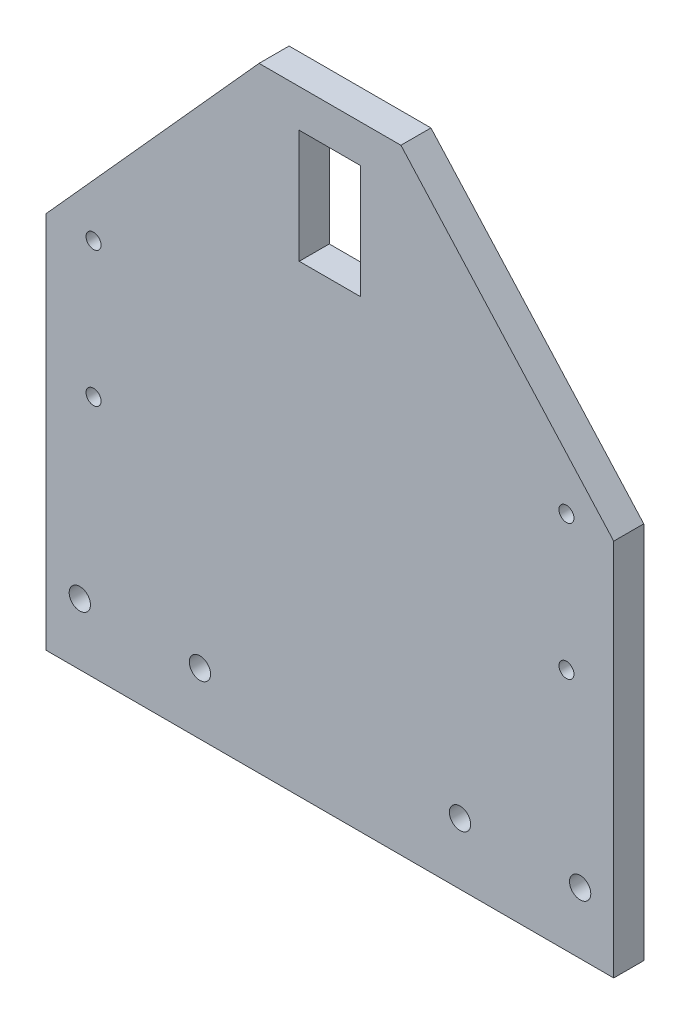
SolidWorks part; units mm, degrees
material "Cast Alloy Steel"
ref_plane "Front Plane" through (0, 0, 0) normal (0, 0, 1) x (1, 0, 0)
ref_plane "Top Plane" through (0, 0, 0) normal (0, 1, 0) x (1, 0, 0)
ref_plane "Right Plane" through (0, 0, 0) normal (1, 0, 0) x (0, 0, -1)
sketch "Sketch1" plane through (0, 0, 0) normal (0, 0, 1) x (1, 0, 0)
  line L0 (60, 0) -> (-60, 0)
  line L1 (0, 80) -> (0, 0) construction
  line L2 (-60, 0) -> (-60, 80)
  line L3 (60, 0) -> (60, 80)
  line L4 (60, 80) -> (15, 130)
  line L5 (15, 130) -> (-15, 130)
  line L6 (-15, 130) -> (-60, 80)
  point P3 (0, 130)
  dimension "D2" = 50
  dimension "D3" = 80
  dimension "D1" = 60
  dimension "D4" = 45
extrude "Boss-Extrude1" add sketch "Sketch1" along normal mid plane 6.35
sketch "Sketch3" plane through (0, 0, 3.175) normal (0, 0, 1) x (1, 0, 0)
  line L0 (15, 130) -> (-15, 130) construction
  line L1 (-60, 0) -> (60, 0) construction
  line L2 (0, 0) -> (0, 12.5) construction
  line L3 (-6.5, 98) -> (6.5, 98)
  line L4 (-6.5, 98) -> (-6.5, 122)
  line L5 (-6.5, 122) -> (6.5, 122)
  line L6 (6.5, 98) -> (6.5, 122)
  line L7 (-6.5, 98) -> (6.5, 122) construction
  line L8 (-6.5, 122) -> (6.5, 98) construction
  line L9 (-50, 80) -> (-50, 51.425) construction
  line L10 (0, 76.1055) -> (0, 45.0169) construction
  circle A0 centre (-52.9, 13) radius 2.25
  circle A1 centre (-27.5, 13) radius 2.25
  circle A2 centre (27.5, 13) radius 2.25
  circle A3 centre (52.9, 13) radius 2.25
  circle A4 centre (-50, 80) radius 1.5875
  circle A5 centre (-50, 51.425) radius 1.5875
  circle A6 centre (50, 51.425) radius 1.5875
  circle A7 centre (50, 80) radius 1.5875
  point P13 (0, 110)
  dimension "D4" = 4.5
  dimension "D9" = 3.175
  dimension "D1" = 25.4
  dimension "D2" = 27.5
  dimension "D3" = 13
  dimension "D5" = 13
  dimension "D6" = 24
  dimension "D7" = 20
  dimension "D8" = 28.575
  dimension "D10" = 50
  dimension "D11" = 80
extrude "Cut-Extrude1" cut sketch "Sketch3" against normal through all
